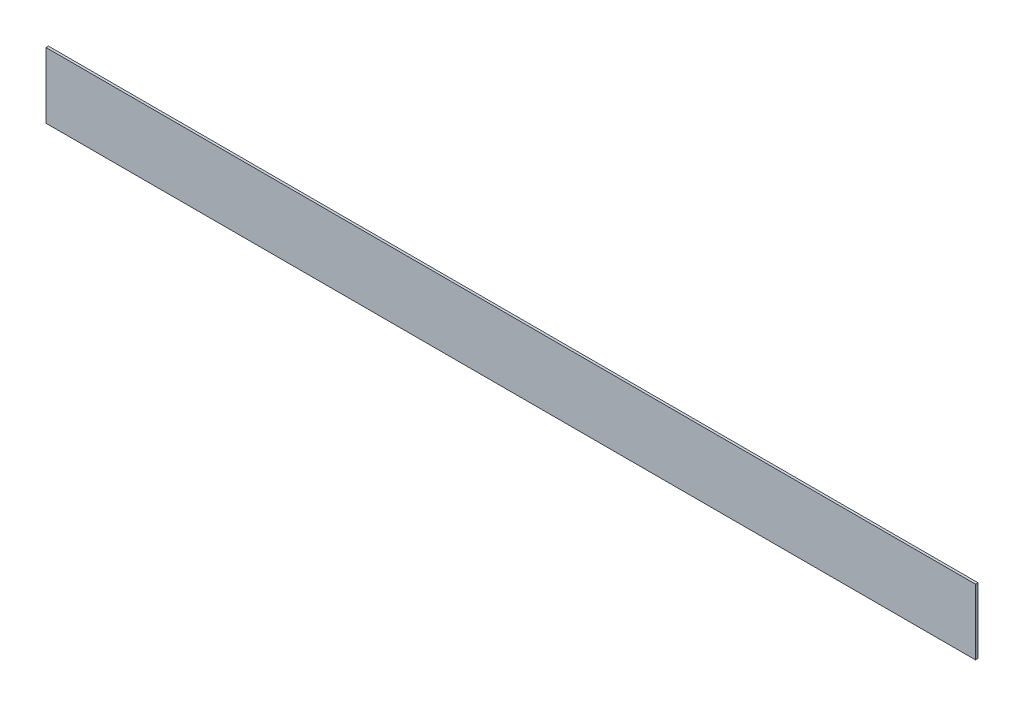
SolidWorks part; units mm, degrees
material "Cedar"
ref_plane "Front Plane" through (0, 0, 0) normal (0, 0, 1) x (1, 0, 0)
ref_plane "Top Plane" through (0, 0, 0) normal (0, 1, 0) x (1, 0, 0)
ref_plane "Right Plane" through (0, 0, 0) normal (1, 0, 0) x (0, 0, -1)
sketch "Sketch1" plane through (0, 0, 0) normal (0, 0, 1) x (1, 0, 0)
  line L1 (-637.9984, 732.6186) -> (866.0016, 732.6186)
  line L2 (-637.9984, 732.6186) -> (-637.9984, 626.4786)
  line L3 (-637.9984, 626.4786) -> (866.0016, 626.4786)
  line L4 (866.0016, 732.6186) -> (866.0016, 626.4786)
  dimension "D1" = 1504
  dimension "D2" = 106.14
extrude "Boss-Extrude1" add sketch "Sketch1" along normal blind 4
